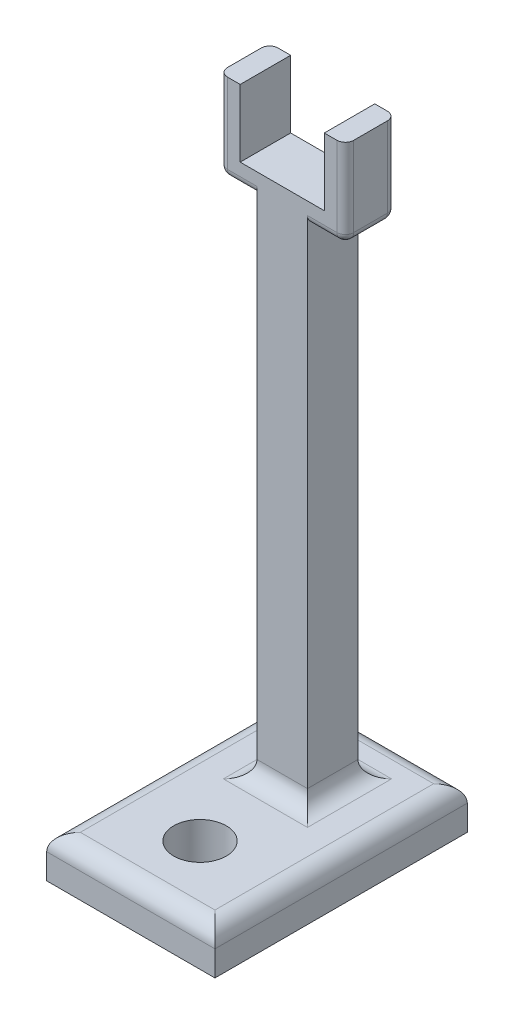
SolidWorks part; units mm, degrees
ref_plane "Front Plane" through (0, 0, 0) normal (0, 0, 1) x (1, 0, 0)
ref_plane "Top Plane" through (0, 0, 0) normal (0, 1, 0) x (1, 0, 0)
ref_plane "Right Plane" through (0, 0, 0) normal (1, 0, 0) x (0, 0, -1)
sketch "Sketch2" plane through (0, 0, 0) normal (0, 1, 0) x (1, 0, 0)
  line L1 (0, 0) -> (25.4, 0)
  line L2 (0, 0) -> (0, 38.1)
  line L3 (0, 38.1) -> (25.4, 38.1)
  line L4 (25.4, 0) -> (25.4, 38.1)
  dimension "D1" = 38.1
  dimension "D2" = 25.4
extrude "Boss-Extrude1" add sketch "Sketch2" along normal blind 6.35
sketch "Sketch3" plane through (0, 6.35, 0) normal (0, 1, 0) x (1, 0, 0)
  line L0 (0, 38.1) -> (0, 0) construction
  line L1 (8.89, 22.86) -> (16.51, 22.86)
  line L2 (8.89, 22.86) -> (8.89, 30.48)
  line L3 (8.89, 30.48) -> (16.51, 30.48)
  line L4 (16.51, 22.86) -> (16.51, 30.48)
  line L5 (25.4, 38.1) -> (0, 38.1) construction
  dimension "D1" = 7.62
  dimension "D2" = 7.62
  dimension "D3" = 8.89
  dimension "D4" = 7.62
extrude "Boss-Extrude2" add sketch "Sketch3" along normal blind 76.2
sketch "Sketch5" plane through (0, 0, -22.86) normal (0, 0, 1) x (1, 0, 0)
  line L0 (8.89, 82.55) -> (16.51, 82.55) construction
  line L1 (3.175, 82.55) -> (22.225, 82.55)
  line L2 (3.175, 82.55) -> (3.175, 95.885)
  line L3 (3.175, 95.885) -> (6.35, 95.885)
  line L4 (22.225, 82.55) -> (22.225, 95.885)
  line L6 (6.35, 95.885) -> (6.35, 85.725)
  line L7 (6.35, 85.725) -> (19.05, 85.725)
  line L8 (19.05, 95.885) -> (19.05, 85.725)
  line L9 (19.05, 95.885) -> (22.225, 95.885)
  line L12 (16.51, 82.55) -> (16.51, 6.35) construction
  dimension "D1" = 19.05
  dimension "D2" = 12.7
  dimension "D3" = 3.175
  dimension "D4" = 3.175
  dimension "D5" = 5.715
  dimension "D6" = 10.16
extrude "Boss-Extrude3" add sketch "Sketch5" against normal blind 7.62
fillet "Fillet1" radius 2.54 8 edges at (8.89, 6.35, -26.67) (12.7, 6.35, -30.48) (12.7, 6.35, -22.86) (16.51, 6.35, -26.67) (12.7, 6.35, -38.1) (0, 6.35, -19.05) (12.7, 6.35, 0) (25.4, 6.35, -19.05)
sketch "Sketch6" plane through (0, 6.35, 0) normal (0, 1, 0) x (1, 0, 0)
  line L0 (0, 0) -> (0, 38.1) construction
  circle A0 centre (12.7, 10.4462) radius 3.9688
  dimension "D2" = 7.9375
  dimension "D1" = 12.7
extrude "Cut-Extrude1" cut sketch "Sketch6" against normal blind 12.7
fillet "Fillet2" radius 1.27 10 edges at (3.175, 82.55, -26.67) (3.175, 89.2175, -22.86) (3.175, 89.2175, -30.48) (6.0325, 82.55, -30.48) (6.0325, 82.55, -22.86) (19.3675, 82.55, -22.86) (19.3675, 82.55, -30.48) (22.225, 82.55, -26.67) (22.225, 89.2175, -22.86) (22.225, 89.2175, -30.48)
